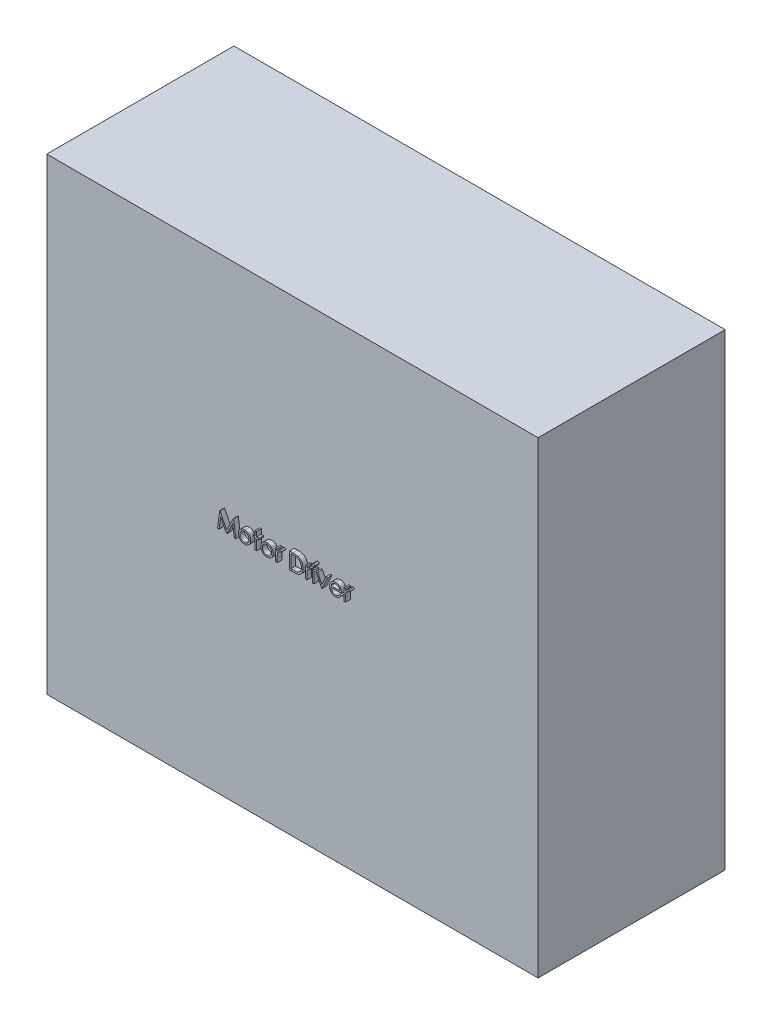
SolidWorks part; units mm, degrees
ref_plane "Front Plane" through (0, 0, 0) normal (0, 0, 1) x (1, 0, 0)
ref_plane "Top Plane" through (0, 0, 0) normal (0, 1, 0) x (1, 0, 0)
ref_plane "Right Plane" through (0, 0, 0) normal (1, 0, 0) x (0, 0, -1)
sketch "Sketch1" plane through (0, 0, 0) normal (0, 0, 1) x (1, 0, 0)
  line L5 (-52.5, -50) -> (52.5, -50)
  line L6 (-52.5, -50) -> (-52.5, 50)
  line L7 (-52.5, 50) -> (52.5, 50)
  line L8 (52.5, -50) -> (52.5, 50)
  line L9 (0, 50) -> (0, -50) construction
  line L10 (-52.5, 0) -> (52.5, 0) construction
  point P0 (0, 0)
  dimension "D1" = 100
  dimension "D2" = 105
extrude "Boss-Extrude1" add sketch "Sketch1" along normal blind 40
sketch "Sketch3" plane through (0, 0, 40) normal (0, 0, 1) x (1, 0, 0)
sketch "Sketch6" plane through (0, 0, 40) normal (0, 0, 1) x (1, 0, 0)
  text T0 "Motor Driver "
extrude "Boss-Extrude2" add sketch "Sketch6" along normal blind 1
